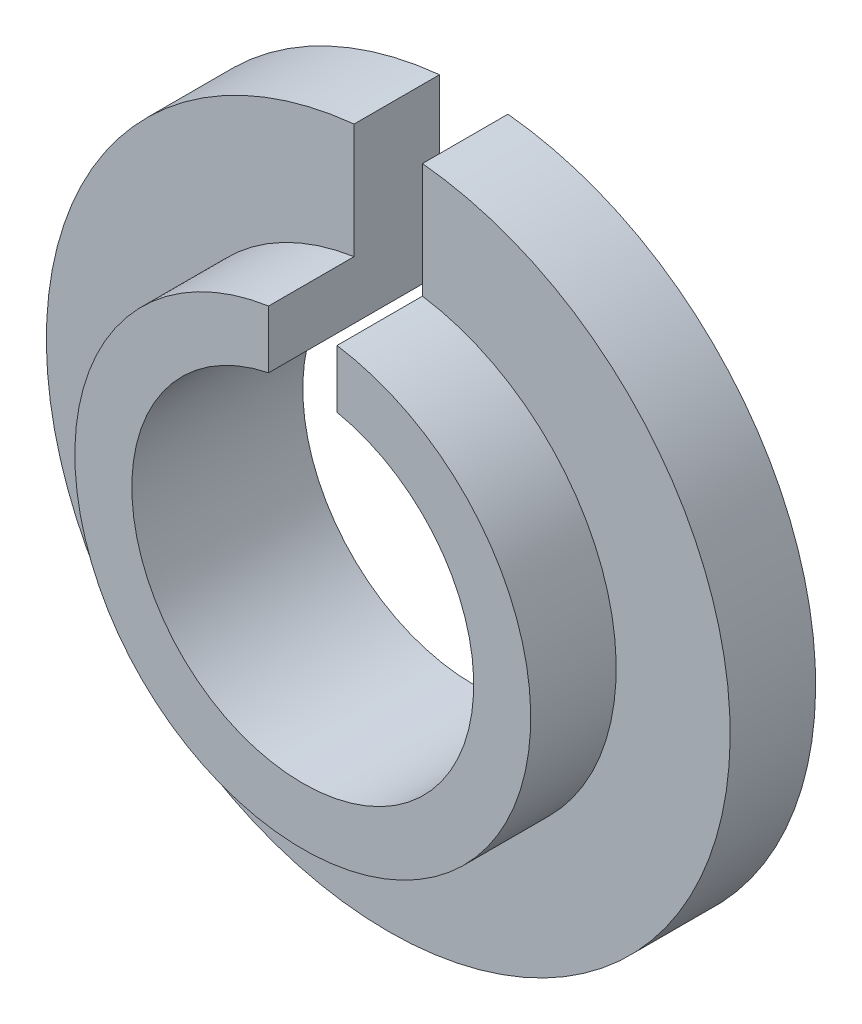
SolidWorks part; units mm, degrees
ref_plane "Front Plane" through (0, 0, 0) normal (0, 0, 1) x (1, 0, 0)
ref_plane "Top Plane" through (0, 0, 0) normal (0, 1, 0) x (1, 0, 0)
ref_plane "Right Plane" through (0, 0, 0) normal (1, 0, 0) x (0, 0, -1)
sketch "Sketch1" plane through (0, 0, 0) normal (0, 0, 1) x (1, 0, 0)
  circle A0 centre (0, 0) radius 15
  circle A1 centre (0, 0) radius 20
  dimension "D1" = 30
  dimension "D2" = 40
extrude "Boss-Extrude1" add sketch "Sketch1" along normal blind 15
sketch "Sketch2" plane through (0, 0, 0) normal (0, 0, -1) x (-1, 0, 0)
  circle A0 centre (0, 0) radius 30
  circle M1 centre (0, 0) radius 20
  dimension "D1" = 60
extrude "Boss-Extrude2" add sketch "Sketch2" against normal blind 7.5 contours A0 M1
sketch "Sketch3" plane through (0, 0, 0) normal (0, 0, 1) x (1, 0, 0)
  line L1 (-3, 0) -> (3, 0)
  line L2 (-3, 0) -> (-3, 34.3278)
  line L3 (-3, 34.3278) -> (3, 34.3278)
  line L4 (3, 0) -> (3, 34.3278)
  dimension "D1" = 3
  dimension "D2" = 6
extrude "Cut-Extrude1" cut sketch "Sketch3" along normal through all
